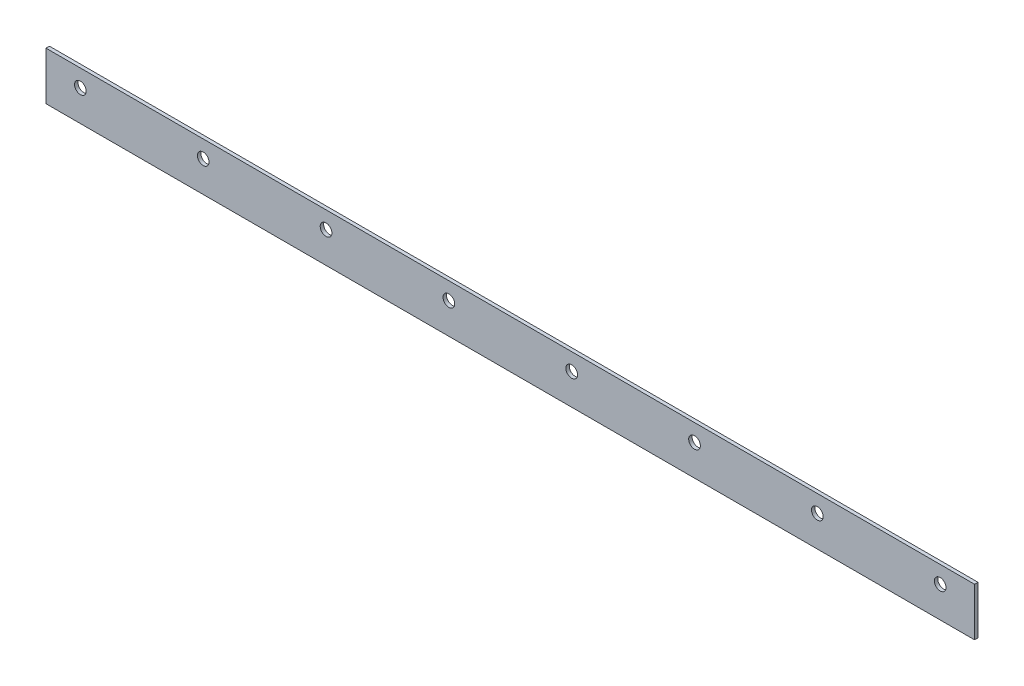
SolidWorks part; units mm, degrees
material "Silicon Rubber"
ref_plane "Front Plane" through (0, 0, 0) normal (0, 0, 1) x (1, 0, 0)
ref_plane "Top Plane" through (0, 0, 0) normal (0, 1, 0) x (1, 0, 0)
ref_plane "Right Plane" through (0, 0, 0) normal (1, 0, 0) x (0, 0, -1)
sketch "Sketch1" plane through (0, 0, 0) normal (0, 0, 1) x (1, 0, 0)
  line L1 (135, -7) -> (-135, -7)
  line L2 (135, -7) -> (135, 7)
  line L3 (135, 7) -> (-135, 7)
  line L4 (-135, -7) -> (-135, 7)
  line L5 (135, -7) -> (-135, 7) construction
  line L6 (135, 7) -> (-135, -7) construction
  point P0 (0, 0)
  dimension "D1" = 14
  dimension "D2" = 270
extrude "Boss-Extrude1" add sketch "Sketch1" along normal blind 1
hole_wizard "M3 Clearance Hole1" positions "Sketch2" profile "Sketch3" hole size "M3" standard "ISO" end condition through all
sketch "Sketch2" plane through (0, 0, 1) normal (0, 0, 1) x (1, 0, 0)
  line L1 (135, -3) -> (101.9207, -3) construction
  line L2 (135, -7) -> (135, 7) construction
  line L4 (-135, -7) -> (135, -7) construction
  point P0 (125, 2)
  dimension "D2" = 4
  dimension "D4" = 5
sketch "Sketch3" plane through (125, 2, 1) normal (1, 0, 0) x (0, -1, 0)
  line L0 (0, 0) -> (0, 1)
  line L1 (0, 1) -> (1.7, 1)
  line L2 (1.7, 1) -> (1.7, 0)
  line L5 (1.7, 0) -> (0, 0)
  line L11 (0, -6.35) -> (0, 107.95) construction
  dimension "Thru Hole Dia." = 3.4
  dimension "Thru Hole Depth" = 1
pattern_linear "LPattern1" count 8 spacing 35.7143 along (-1, 0, 0) of "M3 Clearance Hole1"
